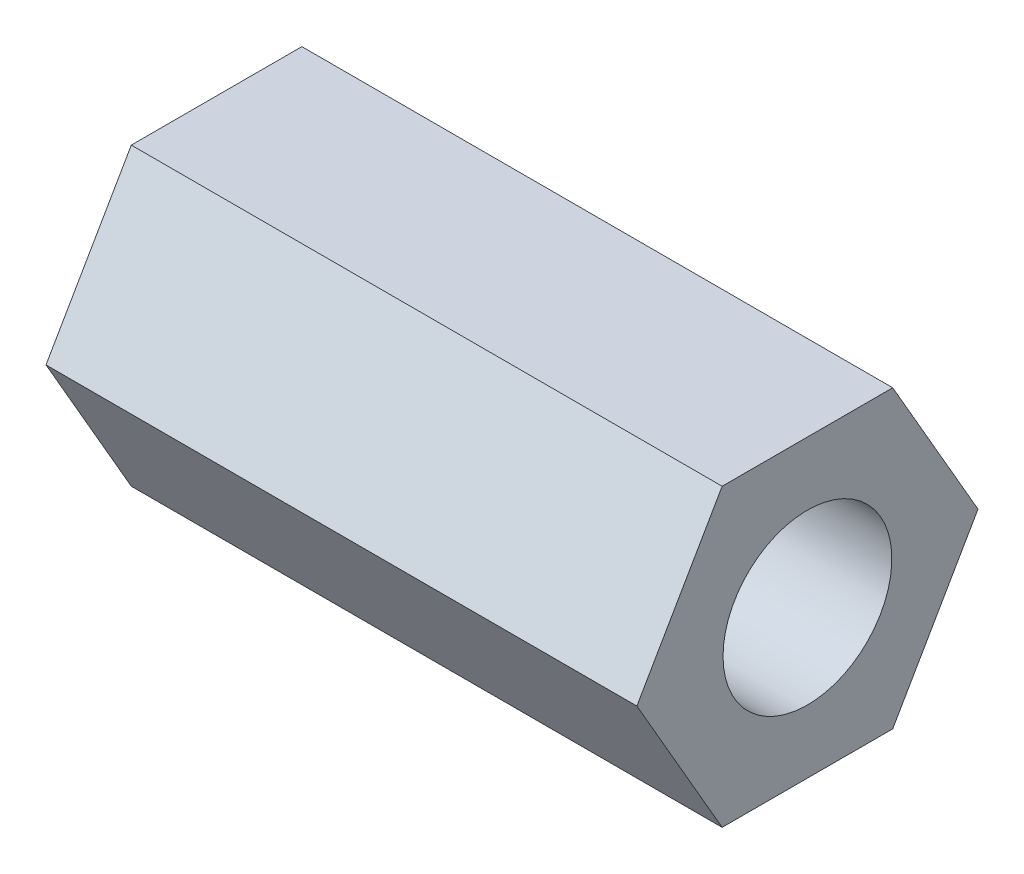
SolidWorks part; units mm, degrees
ref_plane "Front Plane" through (0, 0, 0) normal (0, 0, 1) x (1, 0, 0)
ref_plane "Top Plane" through (0, 0, 0) normal (0, 1, 0) x (1, 0, 0)
ref_plane "Right Plane" through (0, 0, 0) normal (1, 0, 0) x (0, 0, -1)
sketch "Sketch1" plane through (0, 0, 0) normal (1, 0, 0) x (0, 0, -1)
  line L0 (0, 5.5562) -> (0, -5.5562)
  line L1 (6.4158, 0) -> (3.2079, 5.5562)
  line L2 (3.2079, 5.5562) -> (-3.2079, 5.5562)
  line L3 (-3.2079, 5.5562) -> (-6.4158, 0)
  line L4 (-6.4158, 0) -> (-3.2079, -5.5562)
  line L5 (-3.2079, -5.5562) -> (3.2079, -5.5562)
  line L6 (3.2079, -5.5562) -> (6.4158, 0)
  circle A0 centre (0, 0) radius 5.5562 construction
extrude "Boss-Extrude1" add sketch "Sketch1" along normal blind 22.225 contours L4 L5 L0 L2 L3 | L5 L6 L1 L2 L0
sketch "Sketch2" plane through (0, 0, 0) normal (-1, 0, 0) x (0, 0, 1)
  circle A0 centre (0, 0) radius 3.175
  dimension "D1" = 6.35
extrude "Cut-Extrude1" cut sketch "Sketch2" against normal blind 22.225
